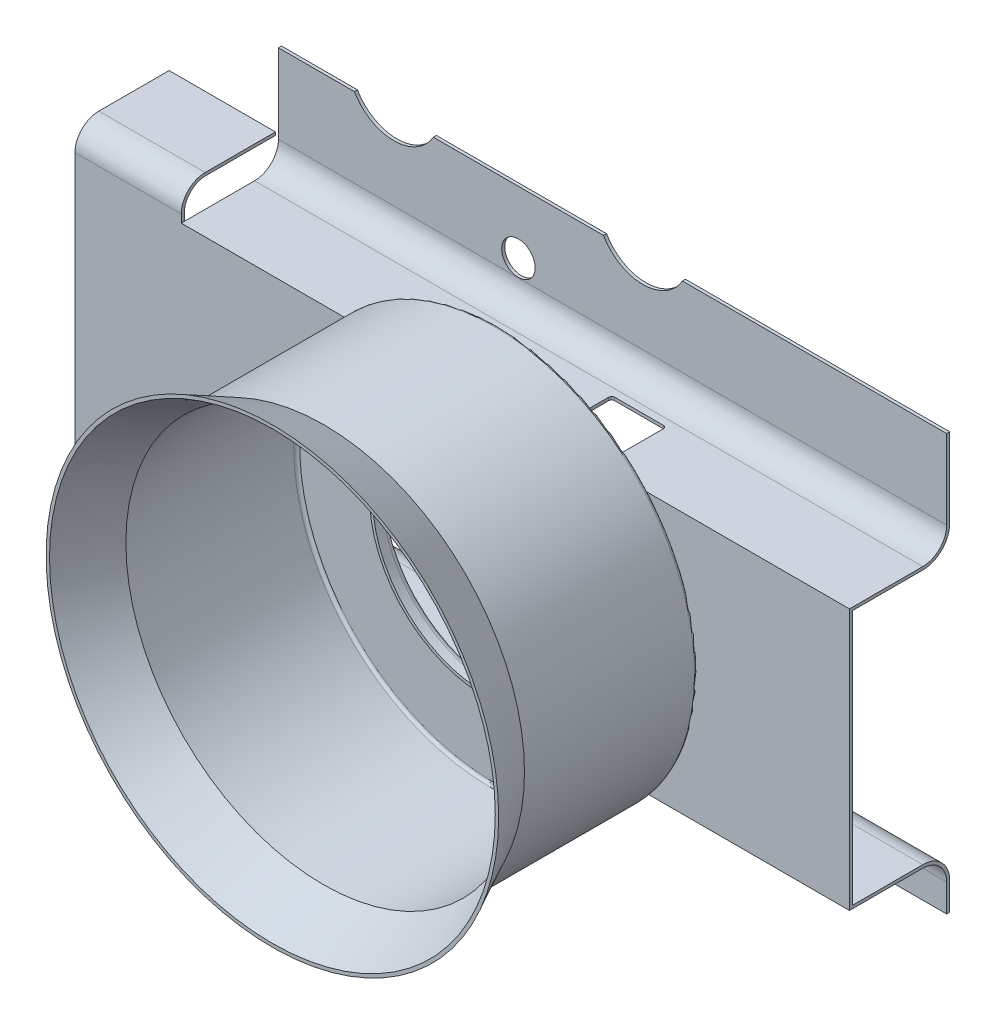
SolidWorks part; units mm, degrees
material "Nickel"
ref_plane "Front Plane" through (0, 0, 0) normal (0, 0, 1) x (1, 0, 0)
ref_plane "Top Plane" through (0, 0, 0) normal (0, 1, 0) x (1, 0, 0)
ref_plane "Right Plane" through (0, 0, 0) normal (1, 0, 0) x (0, 0, -1)
sketch "Sketch2" plane through (0, 0, 0) normal (1, 0, 0) x (0, 0, -1)
  line L0 (-8.9487, 0) -> (28.1795, 0) construction
  line L1 (0, 18.923) -> (4.318, 16.764)
  line L2 (4.318, 16.764) -> (18.542, 16.764)
  line L3 (18.796, 16.51) -> (18.796, 9.398)
  line L4 (18.796, 9.398) -> (17.78, 9.398)
  line L5 (0, 18.923) -> (0, 18.639)
  line L6 (0, 18.639) -> (4.258, 16.51)
  line L7 (4.258, 16.51) -> (18.288, 16.51)
  line L8 (18.542, 16.256) -> (18.542, 9.652)
  line L9 (18.542, 9.652) -> (17.78, 9.652)
  line L12 (17.78, 9.652) -> (17.78, 9.398)
  arc A0 (18.796, 16.51) -> (18.542, 16.764) centre (18.542, 16.51) ccw
  arc A1 (18.542, 16.256) -> (18.288, 16.51) centre (18.288, 16.256) ccw
  point P13 (18.796, 16.764)
  dimension "D7" = 0.254
  dimension "D10" = 0.254
  dimension "D1" = 14.478
  dimension "D2" = 18.923
  dimension "D3" = 18.796
  dimension "D4" = 16.764
  dimension "D5" = 1.016
  dimension "D6" = 9.398
  dimension "D8" = 0.254
  dimension "D9" = 0.254
  dimension "D11" = 0.254
  dimension "D12" = 0.254
revolve "Revolve1" add sketch "Sketch2" angle 360 about L0
ref_plane "Plane1" through (16.764, 0, 0) normal (1, 0, 0) x (0, 0, -1)
sketch "Sketch6" plane through (16.764, 0, 0) normal (1, 0, 0) x (0, 0, -1)
  line L0 (26.924, 19.558) -> (27.178, 19.558)
  line L1 (27.178, 19.558) -> (27.178, 12.922)
  line L2 (24.924, 10.668) -> (19.05, 10.668)
  line L3 (19.05, 10.668) -> (19.05, -10.668)
  line L4 (19.05, -10.668) -> (24.924, -10.668)
  line L5 (27.178, -12.922) -> (27.178, -15.24)
  line L6 (27.178, -15.24) -> (26.924, -15.24)
  line L7 (26.924, -15.24) -> (26.924, -12.922)
  line L8 (24.924, -10.922) -> (18.796, -10.922)
  line L9 (18.796, -10.922) -> (18.796, 10.922)
  line L10 (18.796, 10.922) -> (24.924, 10.922)
  line L12 (26.924, 12.922) -> (26.924, 19.558)
  arc A0 (27.178, 12.922) -> (24.924, 10.668) centre (24.924, 12.922) cw
  arc A1 (24.924, -10.668) -> (27.178, -12.922) centre (24.924, -12.922) cw
  arc A2 (26.924, -12.922) -> (24.924, -10.922) centre (24.924, -12.922) ccw
  arc A4 (24.924, 10.922) -> (26.924, 12.922) centre (24.924, 12.922) ccw
extrude "Boss-Extrude2" add sketch "Sketch6" along normal blind 12.7 separate body
sketch "Sketch8" plane through (16.764, 0, 0) normal (-1, 0, 0) x (0, 0, 1)
  line L12 (-26.924, 12.922) -> (-26.924, 19.558)
  line L13 (-26.924, 19.558) -> (-27.178, 19.558)
  line L14 (-27.178, 19.558) -> (-27.178, 12.922)
  line L15 (-24.924, 10.668) -> (-19.05, 10.668)
  line L16 (-19.05, 10.668) -> (-19.05, -10.668)
  line L17 (-19.05, -10.668) -> (-24.924, -10.668)
  line L18 (-27.178, -12.922) -> (-27.178, -15.24)
  line L19 (-27.178, -15.24) -> (-26.924, -15.24)
  line L20 (-26.924, -15.24) -> (-26.924, -12.922)
  line L21 (-24.924, -10.922) -> (-18.796, -10.922)
  line L22 (-18.796, -10.922) -> (-18.796, 10.922)
  line L23 (-18.796, 10.922) -> (-24.924, 10.922)
  line L24 (-26.924, 12.922) -> (-26.924, 19.558)
  line L25 (-26.924, 19.558) -> (-27.178, 19.558)
  line L26 (-27.178, 19.558) -> (-27.178, 12.922)
  line L27 (-24.924, 10.668) -> (-19.05, 10.668)
  line L28 (-19.05, 10.668) -> (-19.05, -10.668)
  line L29 (-19.05, -10.668) -> (-24.924, -10.668)
  line L30 (-27.178, -12.922) -> (-27.178, -15.24)
  line L31 (-27.178, -15.24) -> (-26.924, -15.24)
  line L32 (-26.924, -15.24) -> (-26.924, -12.922)
  line L33 (-24.924, -10.922) -> (-18.796, -10.922)
  line L34 (-18.796, -10.922) -> (-18.796, 10.922)
  line L35 (-18.796, 10.922) -> (-24.924, 10.922)
  arc A4 (-27.178, 12.922) -> (-24.924, 10.668) centre (-24.924, 12.922) ccw
  arc A5 (-24.924, -10.668) -> (-27.178, -12.922) centre (-24.924, -12.922) ccw
  arc A6 (-24.924, -10.922) -> (-26.924, -12.922) centre (-24.924, -12.922) ccw
  arc A7 (-26.924, 12.922) -> (-24.924, 10.922) centre (-24.924, 12.922) ccw
  arc A8 (-27.178, 12.922) -> (-24.924, 10.668) centre (-24.924, 12.922) ccw
  arc A9 (-24.924, -10.668) -> (-27.178, -12.922) centre (-24.924, -12.922) ccw
  arc A10 (-24.924, -10.922) -> (-26.924, -12.922) centre (-24.924, -12.922) ccw
  arc A11 (-26.924, 12.922) -> (-24.924, 10.922) centre (-24.924, 12.922) ccw
  dimension "D1" = 0
extrude "Boss-Extrude3" add sketch "Sketch8" along normal blind 43.18
sketch "Sketch9" plane through (-26.416, 0, 0) normal (-1, 0, 0) x (0, 0, 1)
  line L0 (-18.796, 11.589) -> (-18.796, -11.589)
  line L1 (-18.796, -10.922) -> (-18.796, 10.922) construction
  line L2 (-20.796, 13.589) -> (-26.67, 13.589)
  line L3 (-20.796, -13.589) -> (-26.67, -13.589)
  line L4 (-26.67, 13.589) -> (-26.67, 13.335)
  line L5 (-26.67, 13.335) -> (-20.8556, 13.335)
  line L6 (-19.05, 11.589) -> (-19.05, -11.589)
  line L7 (-20.796, -13.335) -> (-26.67, -13.335)
  line L8 (-26.67, -13.335) -> (-26.67, -13.589)
  arc A0 (-20.796, -13.589) -> (-18.796, -11.589) centre (-20.796, -11.589) ccw
  arc A1 (-18.796, 11.589) -> (-20.796, 13.589) centre (-20.796, 11.589) ccw
  arc A2 (-20.8556, 13.335) -> (-19.05, 11.589) centre (-20.8556, 11.5283) cw
  arc A3 (-19.05, -11.589) -> (-20.796, -13.335) centre (-20.796, -11.589) cw
  point P4 (-18.796, 0)
  point P10 (-18.796, -13.589)
  point P13 (-18.796, 13.589)
  dimension "D4" = 2
  dimension "D1" = 27.178
  dimension "D2" = 7.874
  dimension "D3" = 7.874
  dimension "D5" = 0.254
  dimension "D6" = 0.254
  dimension "D7" = 0.254
extrude "Boss-Extrude4" add sketch "Sketch9" along normal blind 8.89
sketch "Sketch10" plane through (0, 0, -18.796) normal (0, 0, 1) x (1, 0, 0)
  circle A0 centre (0, 0) radius 9.398
extrude "Cut-Extrude2" cut sketch "Sketch10" against normal blind 9.398
fillet "Fillet1" radius 0.508 1 edges at (0, -9.398, -19.05)
sketch "Sketch11" plane through (0, 0, -27.178) normal (0, 0, -1) x (-1, 0, 0)
  line L0 (26.416, 19.558) -> (26.416, 12.922) construction
  line L2 (26.416, 19.558) -> (-29.464, 19.558) construction
  circle A0 centre (6.35, 14.351) radius 1.397
  dimension "D1" = 2.794
  dimension "D3" = 5.207
  dimension "D2" = 20.066
extrude "Cut-Extrude3" cut sketch "Sketch11" against normal blind 0.254
sketch "Sketch12" plane through (0, 0, -27.178) normal (0, 0, -1) x (-1, 0, 0)
  line L0 (-29.464, 12.922) -> (-29.464, 19.558) construction
  line L1 (26.416, 19.558) -> (26.416, 12.922) construction
  circle A1 centre (16.764, 21.463) radius 3.81
  circle A2 centre (-4.064, 21.463) radius 3.81
  dimension "D1" = 7.62
  dimension "D2" = 21.59
  dimension "D3" = 20.828
  dimension "D4" = 5.842
extrude "Cut-Extrude5" cut sketch "Sketch12" against normal blind 2.54
sketch "Sketch13" plane through (0, 10.922, 0) normal (0, 1, 0) x (1, 0, 0)
  line L0 (29.464, 24.924) -> (29.464, 18.796) construction
  line L1 (4.318, 24.3099) -> (8.382, 24.3099)
  line L2 (4.064, 24.0559) -> (4.064, 19.9919)
  line L3 (4.318, 19.7379) -> (8.382, 19.7379)
  line L4 (8.636, 24.0559) -> (8.636, 19.9919)
  arc A0 (8.382, 24.3099) -> (8.636, 24.0559) centre (8.382, 24.0559) cw
  arc A1 (8.636, 19.9919) -> (8.382, 19.7379) centre (8.382, 19.9919) cw
  arc A2 (4.318, 19.7379) -> (4.064, 19.9919) centre (4.318, 19.9919) cw
  arc A3 (4.064, 24.0559) -> (4.318, 24.3099) centre (4.318, 24.0559) cw
  point P8 (8.636, 24.3099)
  point P11 (8.636, 19.7379)
  point P14 (4.064, 19.7379)
  dimension "D4" = 0.254
  dimension "D1" = 4.572
  dimension "D2" = 4.572
  dimension "D3" = 20.828
extrude "Cut-Extrude6" cut sketch "Sketch13" against normal up to next
